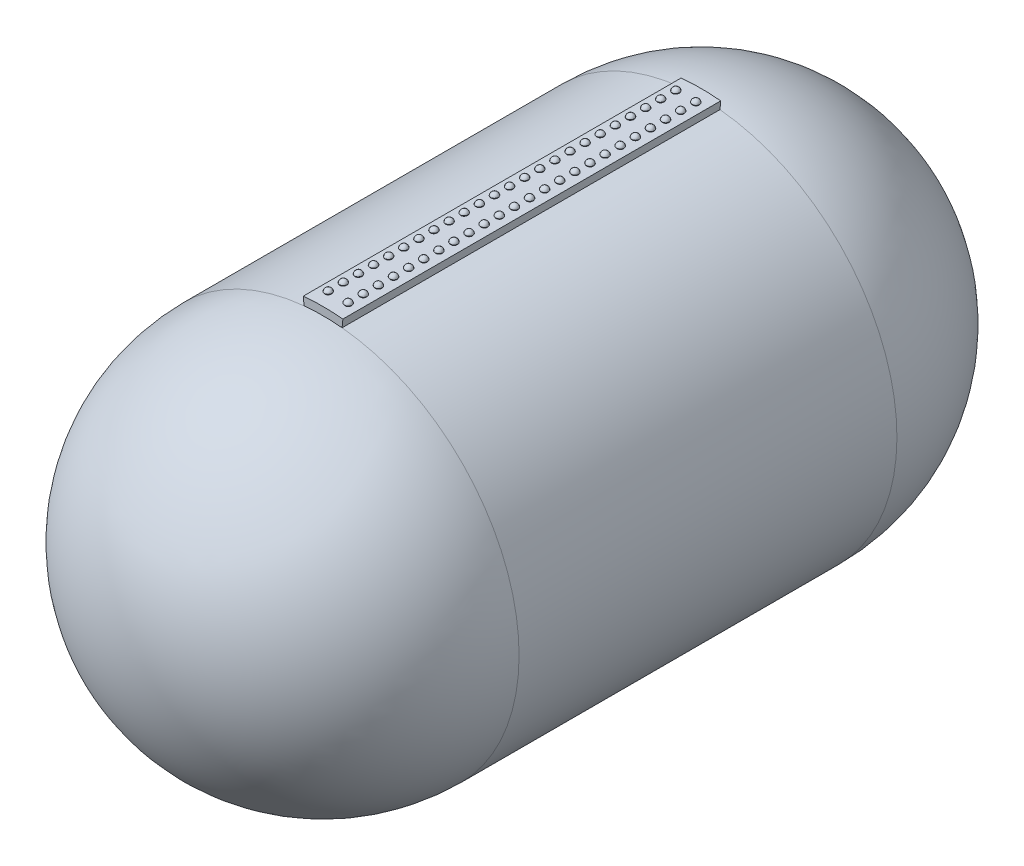
SolidWorks part; units mm, degrees
ref_plane "Front Plane" through (0, 0, 0) normal (0, 0, 1) x (1, 0, 0)
ref_plane "Top Plane" through (0, 0, 0) normal (0, 1, 0) x (1, 0, 0)
ref_plane "Right Plane" through (0, 0, 0) normal (1, 0, 0) x (0, 0, -1)
sketch "Sketch1" plane through (0, 0, 0) normal (0, 0, 1) x (1, 0, 0)
  line L0 (0, 0) -> (0, 1609.5609) construction
  line L1 (-125.8016, 1289.8798) -> (-120.8511, 1239.1207)
  line L2 (125.8016, 1289.8798) -> (120.8511, 1239.1207)
  circle A0 centre (0, 0) radius 1245
  circle A1 centre (0, 0) radius 1200
  arc A2 (125.8016, 1289.8798) -> (-125.8016, 1289.8798) centre (0, 0) ccw
  point P7 (0, 1296)
  dimension "D" = 2400
  dimension "t" = 45
  dimension "outer_strap_thick" = 51
  dimension "right_half_width_of_outer_strap" = 126
  dimension "half_width_outer_strap" = 126
extrude "Boss-Extrude1" add sketch "Sketch1" along normal blind 2400
sketch "Sketch2" plane through (0, 0, 0) normal (0, 0, 1) x (1, 0, 0)
  line L0 (0, 0) -> (-62.9752, 1294.4691) construction
  line L1 (0, 0) -> (62.9752, 1294.4691) construction
  line L2 (-62.9752, 1294.4691) -> (-28.5086, 585.9997) construction
  arc A0 (125.8016, 1289.8798) -> (-125.8016, 1289.8798) centre (0, 0) ccw construction
  point P0 (62.9752, 1294.4691)
  point P1 (-62.9752, 1294.4691)
  point P5 (0, 1296)
  dimension "row1_rytdist_from_center" = 63
  dimension "row_2_rytdist_from_center" = 63
ref_plane "Plane1" through (-62.9752, 1294.4691, 0) normal (-0.0486, 0.9988, 0) x (0.9988, 0.0486, 0)
sketch "Sketch3" plane through (-62.9752, 1294.4691, 0) normal (-0.0486, 0.9988, 0) x (0.9988, 0.0486, 0)
  line L0 (0, 0) -> (0, -2684.229) construction
ref_plane "Plane2" through (0, 0, 96) normal (0, 0, 1) x (1, 0, 0)
sketch "Sketch4" plane through (0, 0, 96) normal (0, 0, 1) x (1, 0, 0)
  line L0 (-62.9752, 1294.4691) -> (-32.9544, 677.385) construction
  line L1 (0, 0) -> (-62.9752, 1294.4691) construction
  line L2 (-62.9752, 1294.4691) -> (-83.9504, 1293.4486)
  line L3 (486.2143, 1321.1868) -> (-612.1646, 1267.7513) construction
  line L4 (-83.9504, 1293.4486) -> (-87.233, 1298.5451)
  line L5 (-87.233, 1298.5451) -> (-63.2303, 1299.7128)
  line L6 (-63.2303, 1299.7128) -> (-62.9752, 1294.4691)
  dimension "rvt_rad" = 21
  dimension "taper_height" = 5.25
  dimension "taper_angle" = 120
revolve "Revolve1" add sketch "Sketch4" angle 360 about L0
sketch "Sketch6" plane through (0, 0, 96) normal (0, 0, 1) x (1, 0, 0)
  line L1 (-39.2276, 1300.8806) -> (-87.233, 1298.5451) construction
  line L3 (-102.3169, 1391.0751) -> (-23.7355, 1199.9605) construction
  line L6 (-87.233, 1298.5451) -> (-83.9504, 1293.4486) construction
  line L7 (-39.2276, 1300.8806) -> (-87.233, 1298.5451) construction
  line L8 (-39.2276, 1300.8806) -> (-87.233, 1298.5451) construction
  line L9 (-63.2303, 1299.7128) -> (-64.2116, 1319.8843)
  line L10 (-39.2276, 1300.8806) -> (-63.2303, 1299.7128)
  line L11 (-63.2303, 1299.7128) -> (-63.0262, 1295.5178) construction
  arc A0 (-39.2276, 1300.8806) -> (-64.2116, 1319.8843) centre (-63.0262, 1295.5178) ccw
  point P0 (-63.0262, 1295.5178)
  point P11 (-63.0262, 1295.5178)
  point P16 (-63.2303, 1299.7128)
  dimension "arc_center_dist" = 4.2
revolve "Revolve2" add sketch "Sketch6" angle 360 about L9
mirror "Mirror1" about plane through (0, 0, 0) normal (1, 0, 0) of bodies 103
pattern_linear "LPattern1" count 24 spacing 96 along (0, 0, 1) of bodies 103
pattern_linear "LPattern2" count 24 spacing 96 along (0, 0, 1) of bodies 104
sketch "Sketch7" plane through (0, 0, 0) normal (1, 0, 0) x (0, 0, -1)
  line L0 (0, 0) -> (0, -1245)
  line L2 (0, 0) -> (1245, 0)
  line L3 (0, -1245) -> (0, 1239.1207) construction
  arc A0 (0, -1245) -> (1245, 0) centre (0, 0) ccw
revolve "Revolve3" add sketch "Sketch7" angle 360 about L2
ref_plane "Plane3" through (0, 0, 1200) normal (0, 0, 1) x (1, 0, 0)
mirror "Mirror2" about plane through (0, 0, 1200) normal (0, 0, 1) of "Revolve3"
